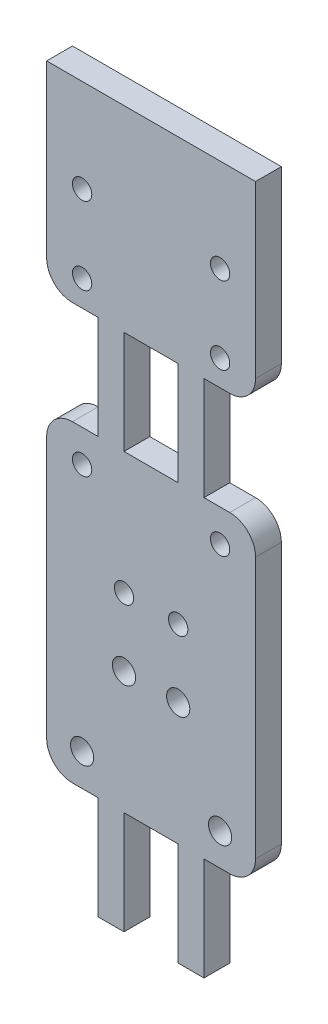
SolidWorks part; units mm, degrees
ref_plane "Front Plane" through (0, 0, 0) normal (0, 0, 1) x (1, 0, 0)
ref_plane "Top Plane" through (0, 0, 0) normal (0, 1, 0) x (1, 0, 0)
ref_plane "Right Plane" through (0, 0, 0) normal (1, 0, 0) x (0, 0, -1)
sketch "Sketch1" plane through (0, 0, 0) normal (0, 0, 1) x (1, 0, 0)
  line L0 (4, 44.7) -> (4, 52.7)
  line L1 (0, -0.06) -> (16.2, -0.06) construction
  line L2 (8.1, -0.06) -> (8.1, 67.93) construction
  line L3 (6, 12.44) -> (10.2, 12.44) construction
  line L4 (6, 20.44) -> (10.2, 20.44)
  line L5 (6, 44.7) -> (6, 52.7)
  line L6 (0, 54.7) -> (0, 67.93)
  line L7 (6, 44.7) -> (10.2, 44.7)
  line L8 (6, 52.7) -> (10.2, 52.7)
  line L9 (2, 44.7) -> (4, 44.7)
  line L10 (0, 67.93) -> (16.2, 67.93)
  line L11 (2, 20.44) -> (4, 20.44)
  line L12 (0, 22.44) -> (0, 42.7)
  line L13 (16.2, 12.44) -> (12.2, 12.44) construction
  line L14 (12.2, 20.44) -> (12.2, 12.44)
  line L15 (10.2, 12.44) -> (10.2, 20.44)
  line L16 (16.2, 12.44) -> (16.2, -0.06) construction
  line L17 (14.2, 52.7) -> (12.2, 52.7)
  line L18 (16.2, 22.44) -> (16.2, 42.7)
  line L19 (14.2, 20.44) -> (12.2, 20.44)
  line L20 (14.2, 44.7) -> (12.2, 44.7)
  line L21 (16.2, 54.7) -> (16.2, 67.93)
  line L22 (10.2, 44.7) -> (10.2, 52.7)
  line L23 (12.2, 44.7) -> (12.2, 52.7)
  line L24 (4, 12.44) -> (6, 12.44)
  line L25 (10.2, 12.44) -> (12.2, 12.44)
  line L36 (2, 52.7) -> (4, 52.7)
  line L46 (0, 12.44) -> (0, -0.06) construction
  line L47 (6, 12.44) -> (6, 20.44)
  line L48 (4, 20.44) -> (4, 12.44)
  line L49 (0, 12.44) -> (4, 12.44) construction
  circle A0 centre (2.75, 60.7) radius 0.75
  circle A1 centre (13.35, 9.94) radius 0.9 construction
  circle A2 centre (13.35, 3.94) radius 0.9 construction
  circle A3 centre (13.45, 54.7) radius 0.75
  arc A4 (16.2, 54.7) -> (14.2, 52.7) centre (14.2, 54.7) cw
  circle A5 centre (13.45, 42.2) radius 0.75
  circle A6 centre (13.45, 22.94) radius 0.9
  circle A7 centre (10.2, 29.94) radius 0.9
  arc A8 (16.2, 22.44) -> (14.2, 20.44) centre (14.2, 22.44) cw
  circle A9 centre (6, 35.2) radius 0.75
  arc A10 (14.2, 44.7) -> (16.2, 42.7) centre (14.2, 42.7) cw
  circle A11 centre (13.45, 60.7) radius 0.75
  circle A12 centre (10.2, 35.2) radius 0.75
  arc A27 (2, 44.7) -> (0, 42.7) centre (2, 42.7) ccw
  arc A31 (0, 22.44) -> (2, 20.44) centre (2, 22.44) ccw
  circle A33 centre (6, 29.94) radius 0.9
  circle A35 centre (2.75, 22.94) radius 0.9
  circle A37 centre (2.75, 42.2) radius 0.75
  arc A43 (0, 54.7) -> (2, 52.7) centre (2, 54.7) ccw
  circle A45 centre (2.75, 54.7) radius 0.75
  circle A46 centre (2.85, 3.94) radius 0.9 construction
  circle A47 centre (2.85, 9.94) radius 0.9 construction
  point P30 (8.1, 20.44)
  point P31 (8.1, 12.44)
  point P47 (8.1, 52.7)
  point P48 (8.1, 44.7)
  dimension "D10" = 1.8
  dimension "D11" = 2
  dimension "D18" = 2
  dimension "D26" = 2
  dimension "D28" = 6
  dimension "D1" = 8
  dimension "D2" = 8
  dimension "D3" = 4
  dimension "D4" = 6
  dimension "D5" = 2.5
  dimension "D6" = 4
  dimension "D7" = 2.85
  dimension "D8" = 2.85
  dimension "D9" = 2
  dimension "D12" = 2.5
  dimension "D13" = 2.75
  dimension "D14" = 9.5
  dimension "D15" = 6
  dimension "D16" = 2
  dimension "D17" = 2
  dimension "D19" = 2.5
  dimension "D20" = 2.75
  dimension "D21" = 2
  dimension "D22" = 2
  dimension "D23" = 2.75
  dimension "D24" = 24.26
  dimension "D25" = 9.5
  dimension "D27" = 2
  dimension "D29" = 2
  dimension "D30" = 2.75
  dimension "D31" = 8.1
  dimension "D32" = 15.23
  dimension "D33" = 6
extrude "Boss-Extrude1" add sketch "Sketch1" along normal blind 2
sketch "Sketch2" plane through (0, 0, 2) normal (0, 0, 1) x (1, 0, 0)
  line L0 (12.2, 12.44) -> (4, 12.44)
  line L1 (4, 20.44) -> (12.2, 20.44)
  line L2 (12.2, 20.44) -> (12.2, 12.44)
  line L3 (4, 12.44) -> (4, 20.44)
  line L4 (4, 52.7) -> (12.2, 52.7)
  line L5 (12.2, 52.7) -> (12.2, 44.7)
  line L6 (12.2, 44.7) -> (4, 44.7)
  line L7 (4, 44.7) -> (4, 52.7)
extrude "Cut-Extrude1" [suppressed] cut sketch "Sketch2" against normal up to surface (2 mm away)
equation "\"D24@Sketch1\"= \"HL@parametersSketch@prostheticParameters.SLDPRT\" * 0.196 - 4 - 8'Thumb PIP Length"
equation "\"D32@Sketch1\" = \"HL@parametersSketch@prostheticParameters.SLDPRT\" * 0.158 - 4 - 10'Thumb DIP Length - Gap Fingertip"
equation "\"D31@Sketch1\"= \"fingerWidth@parametersSketch@prostheticParameters.SLDPRT\" / 2'Finger Width"
equation "\"D10@Sketch1\"= 1.5 + \"tol1@parametersSketch@prostheticParameters.SLDPRT\""
